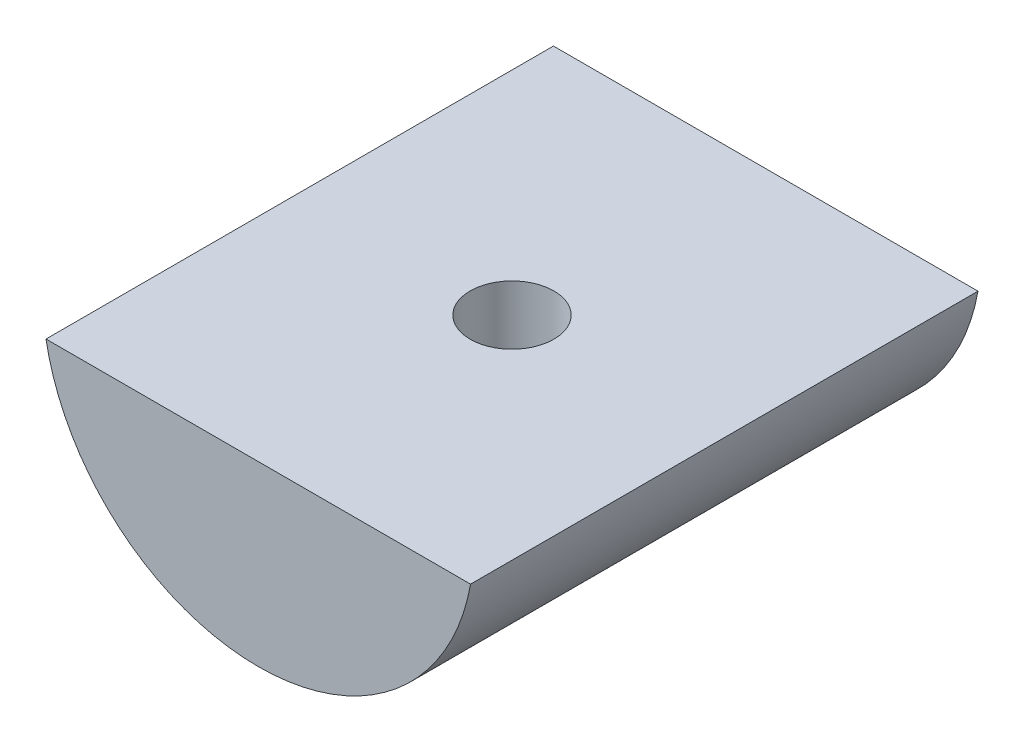
SolidWorks part; units mm, degrees
ref_plane "Front Plane" through (0, 0, 0) normal (0, 0, 1) x (1, 0, 0)
ref_plane "Top Plane" through (0, 0, 0) normal (0, 1, 0) x (1, 0, 0)
ref_plane "Right Plane" through (0, 0, 0) normal (1, 0, 0) x (0, 0, -1)
sketch "Sketch1" plane through (0, 0, 0) normal (0, 0, 1) x (1, 0, 0)
  line L0 (-8.3666, -1.5) -> (8.3666, -1.5)
  arc A0 (-8.3666, -1.5) -> (8.3666, -1.5) centre (0, 0) ccw
  dimension "D1" = 17
  dimension "D2" = 1.5
extrude "Boss-Extrude1" add sketch "Sketch1" along normal blind 20
sketch "Sketch2" plane through (0, -1.5, 0) normal (0, 1, 0) x (1, 0, 0)
  circle A0 centre (0, -10) radius 1.65
  dimension "D2" = 3.3
  dimension "D1" = 10
extrude "Cut-Extrude1" cut sketch "Sketch2" against normal through all
